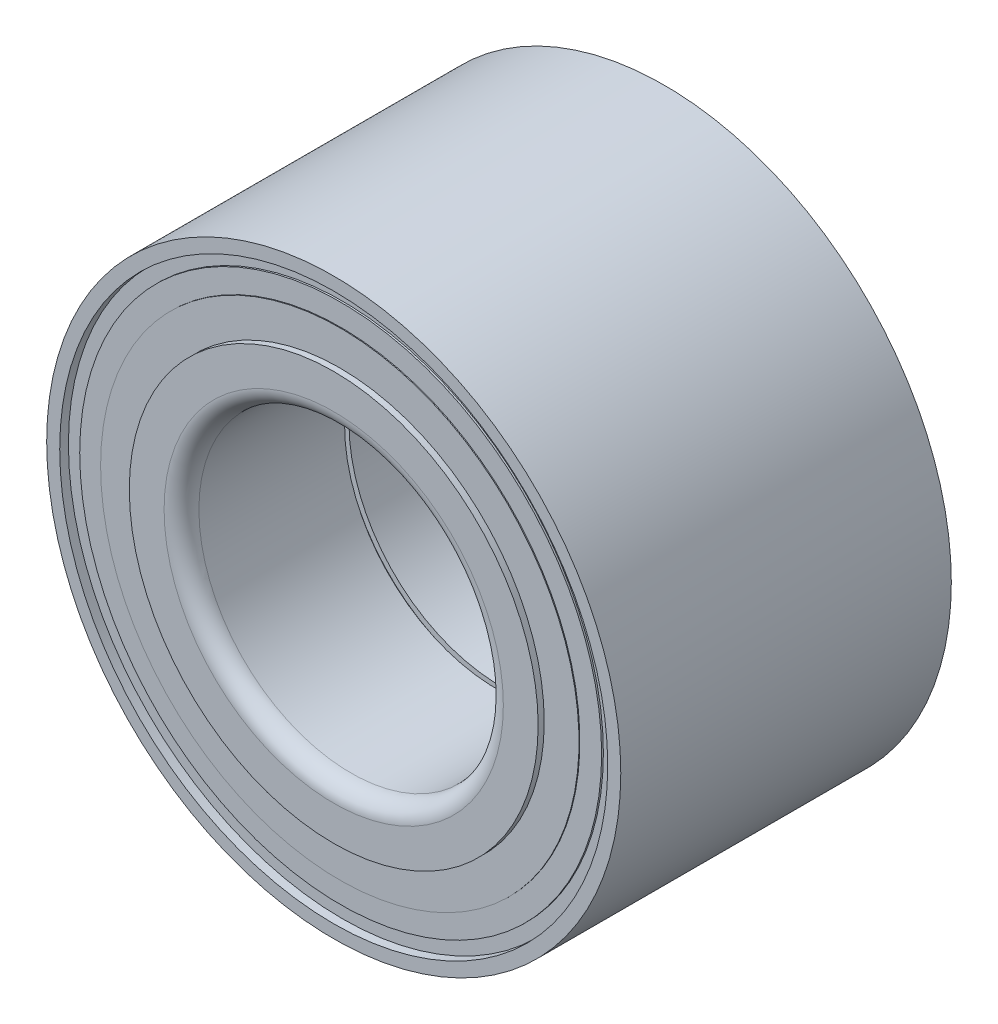
SolidWorks part; units mm, degrees
ref_plane "Alzado" through (0, 0, 0) normal (0, 0, 1) x (1, 0, 0)
ref_plane "Planta" through (0, 0, 0) normal (0, 1, 0) x (1, 0, 0)
ref_plane "Vista lateral" through (0, 0, 0) normal (1, 0, 0) x (0, 0, -1)
sketch "Croquis1" plane through (0, 0, 0) normal (0, 0, 1) x (1, 0, 0)
  circle A0 centre (0, 0) radius 33
  circle A1 centre (0, 0) radius 17.5
  dimension "D1" = 35
  dimension "D2" = 66
extrude "Saliente-Extruir1" add sketch "Croquis1" along normal mid plane 38
sketch "Croquis2" plane through (0, 0, 0) normal (0, 1, 0) x (1, 0, 0)
  line L0 (0, 0) -> (0, 21.9568) construction
  line L1 (17.5, 19) -> (-17.5, 19) construction
  line L2 (17.5, 19) -> (-17.5, 19) construction
  line L3 (17.5, 19) -> (17.5, 0) construction
  line L4 (17.5, 0) -> (0, 0) construction
  line L5 (17.75, 0.5) -> (18.5, 0.5)
  line L6 (18.5, 0.5) -> (18.5, -0.5)
  line L7 (18.5, -0.5) -> (17.75, -0.5)
  line L8 (17.5, -0.25) -> (17.5, 0.25)
  arc A0 (17.75, -0.5) -> (17.5, -0.25) centre (17.75, -0.25) cw
  arc A1 (17.75, 0.5) -> (17.5, 0.25) centre (17.75, 0.25) ccw
  point P14 (17.5, 0.5)
  dimension "D3" = 0.25
  dimension "D1" = 1
  dimension "D2" = 1
revolve "Cortar-Revolución1" cut sketch "Croquis2" angle 360 about L0
fillet "Redondeo1" radius 2 1 edges at (17.5, 0, 19)
sketch "Croquis3" plane through (0, 0, 0) normal (1, 0, 0) x (0, 0, -1)
  line L0 (0, 0) -> (-47.0104, 0) construction
  line L1 (-19, 19.5) -> (-19, -19.5) construction
  line L2 (-19, 19.5) -> (-19, -19.5) construction
  line L3 (-19, 23) -> (-18.5, 23)
  line L5 (-19, 33) -> (-19, -33) construction
  line L6 (-18.5, 23) -> (-19, 23.5)
  line L7 (-19, 23.5) -> (-19, 31.5)
  line L8 (-19, 23.5) -> (-18.3, 23.5)
  line L9 (-18.3, 23.5) -> (-18.3, 27.5)
  line L10 (-18.3, 27.5) -> (-18.2, 27.5)
  line L11 (-18.2, 27.5) -> (-18.2, 30)
  line L12 (-18.2, 30) -> (-18, 30)
  line L13 (-18, 30) -> (-18, 31.5)
  line L14 (-18, 31.5) -> (-19, 31.5)
  line L15 (-19, 23) -> (-19, 23.5)
  dimension "D1" = 1.5
  dimension "D2" = 1
  dimension "D3" = 1.5
  dimension "D4" = 0.2
  dimension "D5" = 0.1
  dimension "D6" = 8
  dimension "D7" = 2.5
  dimension "D8" = 3.5
  dimension "D9" = 0.5
  dimension "D10" = 0.5
revolve "Cortar-Revolución2" cut sketch "Croquis3" angle 360 about L0
fillet "Redondeo2" radius 2 1 edges at (17.5, 0, -19)
mirror "Simetría1" about plane through (0, 0, 0) normal (0, 0, 1) of "Cortar-Revolución2"
